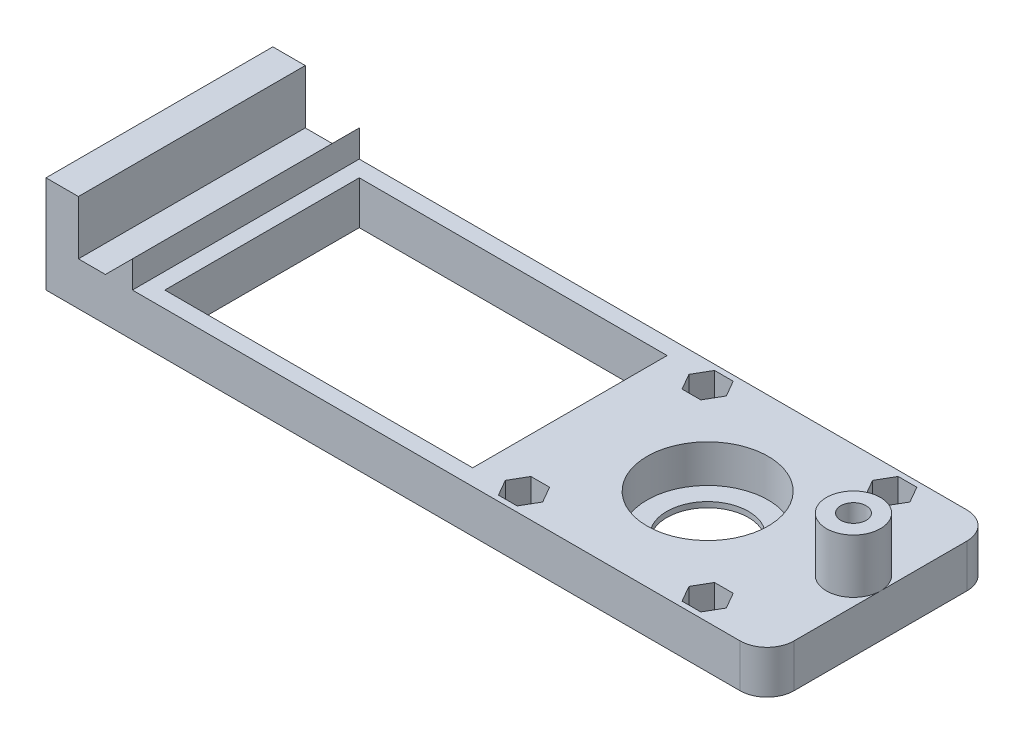
SolidWorks part; units mm, degrees
ref_plane "Front Plane" through (0, 0, 0) normal (0, 0, 1) x (1, 0, 0)
ref_plane "Top Plane" through (0, 0, 0) normal (0, 1, 0) x (1, 0, 0)
ref_plane "Right Plane" through (0, 0, 0) normal (1, 0, 0) x (0, 0, -1)
sketch "Sketch1" plane through (0, 0, 0) normal (0, 1, 0) x (1, 0, 0)
  line L1 (-61.75, -21) -> (61.75, -21)
  line L2 (-61.75, -21) -> (-61.75, 21)
  line L3 (-61.75, 21) -> (61.75, 21)
  line L4 (61.75, -21) -> (61.75, 21)
  line L5 (-61.75, -21) -> (61.75, 21) construction
  line L6 (-61.75, 21) -> (61.75, -21) construction
  point P0 (0, 0)
  dimension "D1" = 123.5
  dimension "D2" = 42
extrude "Boss-Extrude1" add sketch "Sketch1" along normal blind 8
sketch "Sketch2" plane through (0, 8, 0) normal (0, 1, 0) x (1, 0, 0)
  line L0 (61.75, 0) -> (39.75, 0) construction
  line L1 (61.75, -21) -> (61.75, 21) construction
  circle A0 centre (39.75, 0) radius 11.2
  dimension "D2" = 22.4
  dimension "D1" = 22
extrude "Cut-Extrude1" cut sketch "Sketch2" against normal blind 7
sketch "Sketch3" plane through (0, 0, 0) normal (0, -1, 0) x (1, 0, 0)
  line L0 (61.75, 0) -> (39.75, 0) construction
  line L1 (61.75, 21) -> (61.75, -21) construction
  circle A0 centre (39.75, 0) radius 7.55
  dimension "D2" = 15.1
  dimension "D1" = 22
extrude "Cut-Extrude2" cut sketch "Sketch3" against normal up to next
sketch "Sketch9" plane through (0, 8, 0) normal (0, 1, 0) x (1, 0, 0)
  line L0 (56.75, 21) -> (56.75, 17) construction
  line L1 (61.75, 21) -> (-61.75, 21) construction
  line L2 (56.75, 17) -> (61.75, 17) construction
  line L3 (61.75, -21) -> (61.75, 21) construction
  line L4 (61.75, 0) -> (39.75, 0) construction
  line L5 (39.75, 0) -> (39.75, 21) construction
  line L6 (61.75, 21) -> (-61.75, 21) construction
  line L7 (58.4821, 20) -> (55.0179, 20)
  line L8 (55.0179, 20) -> (53.2859, 17)
  line L9 (53.2859, 17) -> (55.0179, 14)
  line L10 (55.0179, 14) -> (58.4821, 14)
  line L11 (58.4821, 14) -> (60.2141, 17)
  line L12 (60.2141, 17) -> (58.4821, 20)
  line L13 (60.2141, -17) -> (58.4821, -20)
  line L14 (58.4821, -20) -> (55.0179, -20)
  line L15 (55.0179, -20) -> (53.2859, -17)
  line L16 (53.2859, -17) -> (55.0179, -14)
  line L17 (55.0179, -14) -> (58.4821, -14)
  line L18 (58.4821, -14) -> (60.2141, -17)
  line L19 (19.2859, 17) -> (21.0179, 20)
  line L20 (21.0179, 20) -> (24.4821, 20)
  line L21 (24.4821, 20) -> (26.2141, 17)
  line L22 (26.2141, 17) -> (24.4821, 14)
  line L23 (24.4821, 14) -> (21.0179, 14)
  line L24 (21.0179, 14) -> (19.2859, 17)
  line L25 (21.0179, -14) -> (19.2859, -17)
  line L26 (24.4821, -14) -> (21.0179, -14)
  line L27 (26.2141, -17) -> (24.4821, -14)
  line L28 (24.4821, -20) -> (26.2141, -17)
  line L29 (21.0179, -20) -> (24.4821, -20)
  line L30 (19.2859, -17) -> (21.0179, -20)
  circle A7 centre (56.75, 17) radius 3 construction
  point P4 (59.3481, 15.5)
  dimension "D3" = 6
  dimension "D1" = 4
  dimension "D2" = 5
  dimension "D4" = 0
extrude "Cut-Extrude4" cut sketch "Sketch9" against normal blind 6
sketch "Sketch10" plane through (0, 0, 0) normal (0, -1, 0) x (1, 0, 0)
  line L0 (56.75, 21) -> (56.75, 17) construction
  line L1 (-61.75, 21) -> (61.75, 21) construction
  line L2 (56.75, 17) -> (61.75, 17) construction
  line L3 (61.75, 21) -> (61.75, -21) construction
  line L4 (39.75, 0) -> (39.75, 21) construction
  line L23 (39.75, 0) -> (61.75, 0) construction
  circle A1 centre (56.75, 17) radius 1.75
  circle A3 centre (22.75, 17) radius 1.75
  circle A4 centre (56.75, -17) radius 1.75
  circle A5 centre (22.75, -17) radius 1.75
  dimension "D3" = 3.5
  dimension "D1" = 4
  dimension "D2" = 5
extrude "Cut-Extrude5" cut sketch "Sketch10" against normal blind 2
sketch "Sketch12" plane through (0, 0, -21) normal (0, 0, -1) x (-1, 0, 0)
  line L0 (55.75, 8) -> (50.75, 8) construction
  line L1 (61.75, 8) -> (55.75, 8)
  line L2 (61.75, 8) -> (61.75, 18)
  line L3 (61.75, 18) -> (55.75, 18)
  line L4 (55.75, 8) -> (55.75, 18)
  line L5 (-61.75, 8) -> (61.75, 8) construction
  line L6 (50.75, 8) -> (45.75, 8)
  line L7 (45.75, 8) -> (45.75, 13)
  line L8 (45.75, 13) -> (50.75, 8)
  dimension "D1" = 10
  dimension "D2" = 6
  dimension "D3" = 5
  dimension "D4" = 5
  dimension "D5" = 5
extrude "Boss-Extrude2" add sketch "Sketch12" against normal up to surface (42 mm away) up to face at (0, 4, 21)
sketch "Sketch13" plane through (0, 8, 0) normal (0, 1, 0) x (1, 0, 0)
  line L0 (-42.75, 21) -> (-42.75, 18) construction
  line L1 (61.75, 21) -> (-45.75, 21) construction
  line L2 (-42.75, 18) -> (-45.75, 18) construction
  line L3 (-45.75, -21) -> (-45.75, 21) construction
  line L5 (-42.75, 18) -> (14.25, 18)
  line L6 (-42.75, 18) -> (-42.75, -18)
  line L7 (-42.75, -18) -> (14.25, -18)
  line L8 (14.25, 18) -> (14.25, -18)
  dimension "D1" = 3
  dimension "D2" = 3
  dimension "D3" = 36
  dimension "D4" = 57
extrude "Cut-Extrude6" cut sketch "Sketch13" against normal through all
sketch "Sketch23" plane through (0, 8, 0) normal (0, 1, 0) x (1, 0, 0)
  line L1 (61.75, 21) -> (71.75, 21)
  line L2 (61.75, 21) -> (61.75, -21)
  line L3 (61.75, -21) -> (71.75, -21)
  line L4 (71.75, 21) -> (71.75, -21)
  dimension "D1" = 42
  dimension "D2" = 10
extrude "Boss-Extrude3" add sketch "Sketch23" against normal blind 8
sketch "Sketch24" plane through (0, 8, 0) normal (0, 1, 0) x (1, 0, 0)
  line L0 (71.75, 0) -> (66.75, 0) construction
  line L1 (71.75, -21) -> (71.75, 21) construction
  circle A0 centre (66.75, 0) radius 5
  dimension "D1" = 5
extrude "Boss-Extrude4" add sketch "Sketch24" along normal blind 10
fillet "Fillet1" radius 5 2 edges at (71.75, 4, -21) (71.75, 4, 21)
sketch "Sketch25" plane through (0, 18, 0) normal (0, 1, 0) x (1, 0, 0)
  line L0 (66.75, 5) -> (66.75, -5) construction
  circle A0 centre (66.75, 0) radius 2.35
  circle A1 centre (66.75, 0) radius 5 construction
  circle A2 centre (66.75, 0) radius 5 construction
  dimension "D1" = 4.7
extrude "Cut-Extrude7" cut sketch "Sketch25" against normal up to surface (18 mm away) up to face at (-14.25, 0, 0)
